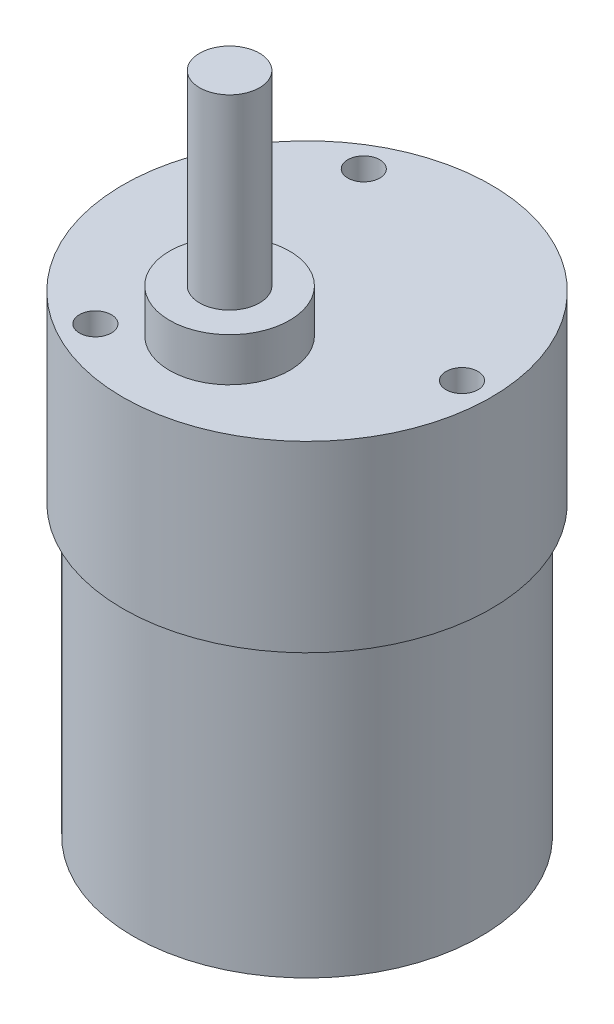
SolidWorks part; units mm, degrees
ref_plane "Front Plane" through (0, 0, 0) normal (0, 0, 1) x (1, 0, 0)
ref_plane "Top Plane" through (0, 0, 0) normal (0, 1, 0) x (1, 0, 0)
ref_plane "Right Plane" through (0, 0, 0) normal (1, 0, 0) x (0, 0, -1)
sketch "Sketch1" plane through (0, 0, 0) normal (0, 1, 0) x (1, 0, 0)
  circle A0 centre (0, 0) radius 17.2593
  dimension "D1" = 34.5186
extrude "Boss-Extrude1" add sketch "Sketch1" along normal blind 28.7528
sketch "Sketch2" plane through (0, 28.7528, 0) normal (0, 1, 0) x (1, 0, 0)
  circle A0 centre (0, 0) radius 18.307
  dimension "D1" = 36.6141
extrude "Boss-Extrude2" add sketch "Sketch2" along normal blind 18.2118
sketch "Sketch3" plane through (0, 46.9646, 0) normal (0, 1, 0) x (1, 0, 0)
  line L0 (0, 15.4126) -> (-13.3477, -7.7063) construction
  line L1 (-13.3477, -7.7063) -> (13.3477, -7.7063) construction
  line L2 (13.3477, -7.7063) -> (0, 15.4126) construction
  line L3 (0, 15.4126) -> (0, -7.7063) construction
  line L4 (13.3477, -7.7063) -> (-6.6738, 3.8531) construction
  line L5 (18.307, 0) -> (-18.307, 0) construction
  line L6 (15.4126, 0) -> (-7.7063, 13.3477) construction
  line L7 (-7.7063, -13.3477) -> (15.4126, 0) construction
  line L8 (-7.7063, 13.3477) -> (-7.7063, -13.3477) construction
  line L9 (15.4126, 0) -> (-7.7063, 0) construction
  line L10 (-7.7063, 13.3477) -> (3.8531, -6.6738) construction
  circle A0 centre (0, 0) radius 18.307 construction
  circle A1 centre (0, -7.7063) radius 5.969 construction
  circle A2 centre (-7.7063, -13.3477) radius 1.5875
  circle A3 centre (-7.7063, 13.3477) radius 1.5875
  circle A4 centre (15.4126, 0) radius 1.5875
  point P10 (0, 0)
  dimension "D2" = 11.938
  dimension "D3" = 3.175
  dimension "D1" = 26.6954
extrude "Cut-Extrude1" cut sketch "Sketch3" against normal blind 12.7
sketch "Sketch4" plane through (0, 46.9646, 0) normal (0, 1, 0) x (1, 0, 0)
  line L0 (0, 15.4126) -> (-13.3477, -7.7063) construction
  line L1 (-13.3477, -7.7063) -> (13.3477, -7.7063) construction
  line L2 (13.3477, -7.7063) -> (0, 15.4126) construction
  line L3 (0, 15.4126) -> (0, -7.7063) construction
  line L4 (13.3477, -7.7063) -> (-6.6738, 3.8531) construction
  line L5 (18.307, 0) -> (-18.3071, 0) construction
  line L6 (15.4126, 0) -> (-7.7063, 13.3477) construction
  line L7 (-7.7063, -13.3477) -> (15.4126, 0) construction
  line L8 (-7.7063, 13.3477) -> (-7.7063, -13.3477) construction
  line L9 (15.4126, 0) -> (-7.7063, 0) construction
  line L10 (-7.7063, 13.3477) -> (3.8531, -6.6738) construction
  circle A0 centre (0, -7.7063) radius 5.969
  circle A1 centre (-7.7063, -13.3477) radius 1.5875 construction
  circle A2 centre (-7.7063, 13.3477) radius 1.5875 construction
  circle A3 centre (15.4126, 0) radius 1.5875 construction
  circle A7 centre (-7.7063, 13.3477) radius 1.5875 construction
  point P7 (0, 0)
  dimension "D2" = 11.938
  dimension "D1" = 26.6954
  dimension "D3" = 36.6141
extrude "Boss-Extrude3" add sketch "Sketch4" along normal blind 4.318
sketch "Sketch5" plane through (0, 51.2826, 0) normal (0, 1, 0) x (1, 0, 0)
  circle A0 centre (0, -7.7063) radius 2.9781
  dimension "D1" = 5.9563
extrude "Boss-Extrude4" add sketch "Sketch5" along normal blind 18.542
